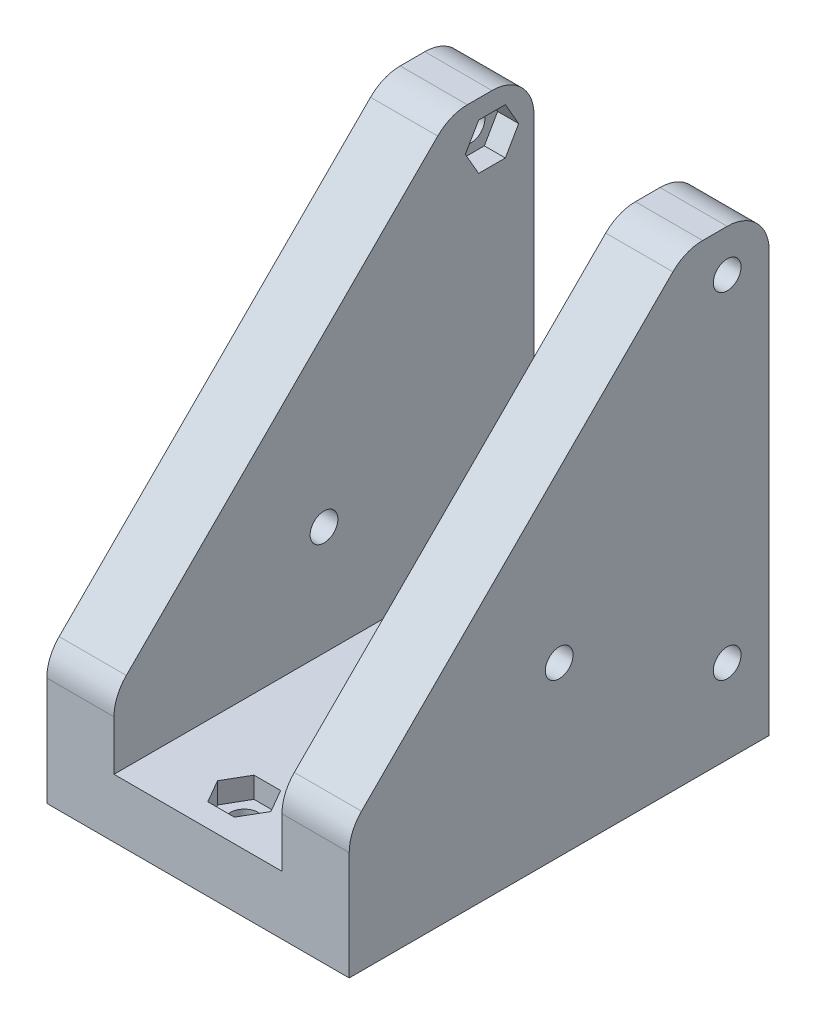
SolidWorks part; units mm, degrees
ref_plane "Přední rovina" through (0, 0, 0) normal (0, 0, 1) x (1, 0, 0)
ref_plane "Horní rovina" through (0, 0, 0) normal (0, 1, 0) x (1, 0, 0)
ref_plane "Pravá rovina" through (0, 0, 0) normal (1, 0, 0) x (0, 0, -1)
sketch "Skica1" plane through (0, 0, 0) normal (0, 0, 1) x (1, 0, 0)
  line L0 (0, 0) -> (0, 55)
  line L1 (0, 55) -> (8, 55)
  line L2 (8, 55) -> (8, 7)
  line L3 (8, 7) -> (28, 7)
  line L4 (28, 7) -> (28, 55)
  line L5 (28, 55) -> (36, 55)
  line L6 (36, 55) -> (36, 0)
  line L7 (36, 0) -> (0, 0)
  dimension "D1" = 20
  dimension "D2" = 8
  dimension "D3" = 8
  dimension "D4" = 7
  dimension "D5" = 55
  dimension "D6" = 55
extrude "Přidat vysunutím1" add sketch "Skica1" along normal blind 50
chamfer "Zkosení1" distance 40 angle 45 1 edges at (32, 55, 50)
chamfer "Zkosení2" distance 40 angle 45 1 edges at (4, 55, 50)
sketch "Skica2" plane through (36, 0, 0) normal (1, 0, 0) x (0, 0, -1)
  line L0 (-10, 55) -> (0, 55) construction
  line L1 (-50, 0) -> (0, 0) construction
  line L2 (0, 0) -> (0, 55) construction
  circle A0 centre (-5, 50) radius 1.65
  circle A1 centre (-5, 10) radius 1.65
  circle A2 centre (-25, 20) radius 1.65
  point P14 (0, 27.5)
  dimension "D1" = 3.3
  dimension "D2" = 3.3
  dimension "D7" = 3.3
  dimension "D3" = 5
  dimension "D4" = 40
  dimension "D5" = 5
  dimension "D6" = 5
  dimension "D8" = 20
  dimension "D9" = 25
extrude "Odebrat vysunutím1" cut sketch "Skica2" against normal through all
fillet "Zaoblit1" radius 5 6 edges at (32, 15, 50) (4, 15, 50) (4, 55, 10) (32, 55, 10) (4, 55, 0) (32, 55, 0)
sketch "Skica3" plane through (28, 0, 0) normal (-1, 0, 0) x (0, 0, 1)
  line L0 (7.9289, 55) -> (5, 55) construction
  line L1 (6.5877, 52.75) -> (3.4123, 52.75)
  line L2 (3.4123, 52.75) -> (1.8246, 50)
  line L3 (1.8246, 50) -> (3.4123, 47.25)
  line L4 (3.4123, 47.25) -> (6.5877, 47.25)
  line L5 (6.5877, 47.25) -> (8.1754, 50)
  line L6 (8.1754, 50) -> (6.5877, 52.75)
  line L8 (6.5877, 12.75) -> (3.4123, 12.75)
  line L9 (3.4123, 12.75) -> (1.8246, 10)
  line L10 (1.8246, 10) -> (3.4123, 7.25)
  line L11 (3.4123, 7.25) -> (6.5877, 7.25)
  line L12 (6.5877, 7.25) -> (8.1754, 10)
  line L13 (8.1754, 10) -> (6.5877, 12.75)
  circle A0 centre (5, 50) radius 2.75 construction
  circle A1 centre (5, 10) radius 2.75 construction
  dimension "D1" = 5.5
  dimension "D2" = 60
  dimension "D3" = 60
  dimension "D4" = 5.5
extrude "Odebrat vysunutím2" cut sketch "Skica3" against normal blind 2.5
sketch "Skica6" plane through (8, 0, 0) normal (1, 0, 0) x (0, 0, -1)
  line L0 (-7.9289, 55) -> (-5, 55) construction
  line L1 (-3.4123, 52.75) -> (-6.5877, 52.75)
  line L2 (-6.5877, 52.75) -> (-8.1754, 50)
  line L3 (-8.1754, 50) -> (-6.5877, 47.25)
  line L4 (-6.5877, 47.25) -> (-3.4123, 47.25)
  line L5 (-3.4123, 47.25) -> (-1.8246, 50)
  line L6 (-1.8246, 50) -> (-3.4123, 52.75)
  line L7 (-3.4123, 12.75) -> (-6.5877, 12.75)
  line L8 (-6.5877, 12.75) -> (-8.1754, 10)
  line L9 (-8.1754, 10) -> (-6.5877, 7.25)
  line L10 (-6.5877, 7.25) -> (-3.4123, 7.25)
  line L11 (-3.4123, 7.25) -> (-1.8246, 10)
  line L12 (-1.8246, 10) -> (-3.4123, 12.75)
  circle A0 centre (-5, 50) radius 2.75 construction
  circle A1 centre (-5, 10) radius 2.75 construction
  dimension "D1" = 60
  dimension "D2" = 60
  dimension "D3" = 5.5
  dimension "D4" = 5.5
extrude "Odebrat vysunutím3" cut sketch "Skica6" against normal blind 2.5
sketch "Skica7" plane through (0, 0, 0) normal (0, -1, 0) x (1, 0, 0)
  line L2 (0, 50) -> (0, 0) construction
  line L6 (0, 0) -> (36, 0) construction
  circle A0 centre (18, 44.5) radius 1.65
  circle A1 centre (18, 25.45) radius 1.65
  circle A2 centre (18, 6.4) radius 1.65
  dimension "D1" = 3.3
  dimension "D2" = 3.3
  dimension "D3" = 3.3
  dimension "D4" = 6.4
  dimension "D5" = 19.05
  dimension "D6" = 19.05
  dimension "D7" = 18
  dimension "D8" = 18
  dimension "D9" = 18
extrude "Odebrat vysunutím4" cut sketch "Skica7" against normal through all
sketch "Skica8" plane through (0, 7, 0) normal (0, 1, 0) x (1, 0, 0)
  line L0 (28, -50) -> (8, -50) construction
  line L1 (14.8246, -6.4) -> (16.4123, -9.15)
  line L2 (16.4123, -9.15) -> (19.5877, -9.15)
  line L3 (19.5877, -9.15) -> (21.1754, -6.4)
  line L4 (21.1754, -6.4) -> (19.5877, -3.65)
  line L5 (19.5877, -3.65) -> (16.4123, -3.65)
  line L6 (16.4123, -3.65) -> (14.8246, -6.4)
  line L7 (14.8246, -25.45) -> (16.4123, -28.2)
  line L8 (16.4123, -28.2) -> (19.5877, -28.2)
  line L9 (19.5877, -28.2) -> (21.1754, -25.45)
  line L10 (21.1754, -25.45) -> (19.5877, -22.7)
  line L11 (19.5877, -22.7) -> (16.4123, -22.7)
  line L12 (16.4123, -22.7) -> (14.8246, -25.45)
  line L13 (14.8246, -44.5) -> (16.4123, -47.25)
  line L14 (16.4123, -47.25) -> (19.5877, -47.25)
  line L15 (19.5877, -47.25) -> (21.1754, -44.5)
  line L16 (21.1754, -44.5) -> (19.5877, -41.75)
  line L17 (19.5877, -41.75) -> (16.4123, -41.75)
  line L18 (16.4123, -41.75) -> (14.8246, -44.5)
  circle A0 centre (18, -6.4) radius 2.75 construction
  circle A1 centre (18, -25.45) radius 2.75 construction
  circle A2 centre (18, -44.5) radius 2.75 construction
  dimension "D1" = 5.5
  dimension "D2" = 5.5
  dimension "D3" = 5.5
  dimension "D4" = 60
  dimension "D5" = 60
  dimension "D6" = 60
extrude "Odebrat vysunutím5" cut sketch "Skica8" against normal blind 2.5
